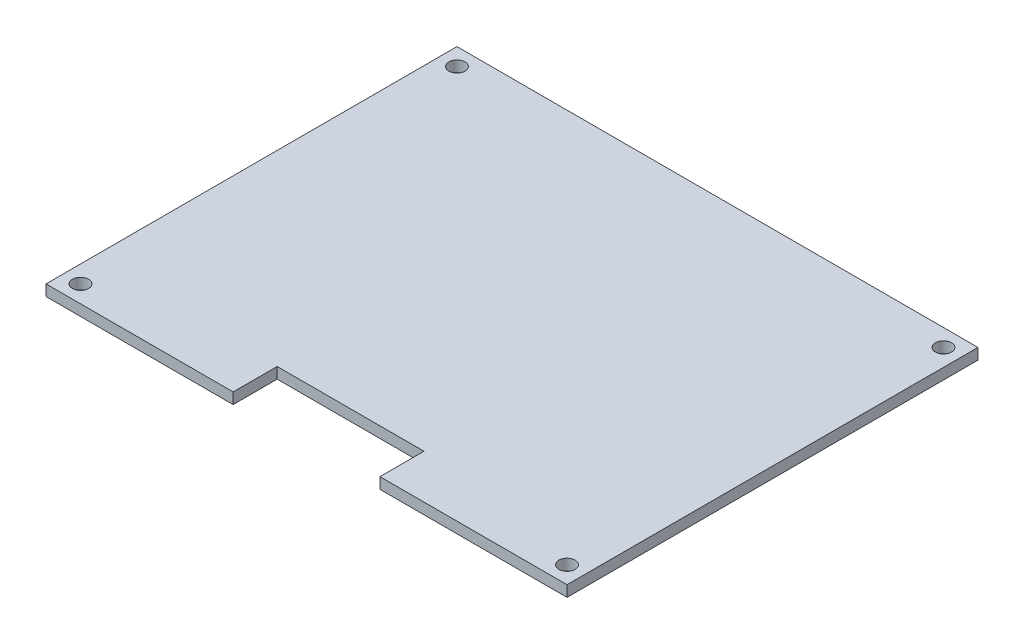
SolidWorks part; units mm, degrees
ref_plane "Front Plane" through (0, 0, 0) normal (0, 0, 1) x (1, 0, 0)
ref_plane "Top Plane" through (0, 0, 0) normal (0, 1, 0) x (1, 0, 0)
ref_plane "Right Plane" through (0, 0, 0) normal (1, 0, 0) x (0, 0, -1)
sketch "Sketch1" plane through (0, 0, 0) normal (0, 1, 0) x (1, 0, 0)
  line L1 (0, 0) -> (71, 0)
  line L2 (0, 0) -> (0, 56)
  line L3 (0, 56) -> (71, 56)
  line L4 (71, 0) -> (71, 56)
  dimension "D1" = 71
  dimension "D2" = 56
extrude "Boss-Extrude1" add sketch "Sketch1" along normal blind 1.5
sketch "Sketch2" plane through (0, 1.5, 0) normal (0, 1, 0) x (1, 0, 0)
  line L0 (0, 0) -> (71, 0) construction
  line L1 (25.5, 6) -> (45.5, 6)
  line L2 (25.5, 6) -> (25.5, 0)
  line L3 (25.5, 0) -> (45.5, 0)
  line L4 (45.5, 6) -> (45.5, 0)
  point P4 (35.5, 0)
  dimension "D1" = 20
  dimension "D2" = 6
extrude "Cut-Extrude1" cut sketch "Sketch2" against normal up to surface (1.5 mm away) up to face at (35.5, 0, -28)
sketch "Sketch5" plane through (0, 1.5, 0) normal (0, 1, 0) x (1, 0, 0)
  line L0 (2.35, 53.65) -> (2.35, 56) construction
  line L1 (71, 56) -> (0, 56) construction
  line L2 (2.35, 56) -> (2.35, 53.65) construction
  line L3 (2.35, 53.65) -> (0, 53.65) construction
  line L4 (0, 56) -> (0, 0) construction
  line L5 (68.65, 53.65) -> (68.65, 56) construction
  line L6 (71, 56) -> (0, 56) construction
  line L7 (68.65, 53.65) -> (71, 53.65) construction
  line L8 (71, 0) -> (71, 56) construction
  circle A0 centre (2.35, 53.65) radius 1.1
  circle A1 centre (68.65, 53.65) radius 1.1
  dimension "D1" = 2.2
  dimension "D3" = 2.35
extrude "Cut-Extrude2" cut sketch "Sketch5" against normal up to surface (1.5 mm away) up to face at (35.5, 0, -15.5)
ref_plane "Plane1" through (0, 0, -28) normal (0, 0, 1) x (1, 0, 0)
mirror "Mirror1" about plane through (0, 0, -28) normal (0, 0, 1) of "Cut-Extrude2"
sketch "Sketch6" plane through (0, 1.5, 0) normal (0, 1, 0) x (1, 0, 0)
  line L0 (63, 40) -> (71, 40) construction
  line L1 (71, 0) -> (71, 56) construction
  line L2 (63, 56) -> (63, 40) construction
  line L3 (71, 56) -> (0, 56) construction
  line L4 (63, 40) -> (63, 28) construction
  line L5 (63, 28) -> (63, 16) construction
  line L6 (0, 56) -> (0, 0) construction
  line L7 (18.45, 13) -> (24.45, 13)
  line L8 (18.45, 13) -> (18.45, 7)
  line L9 (18.45, 7) -> (24.45, 7)
  line L10 (24.45, 13) -> (24.45, 7)
  line L11 (32.5, 13) -> (38.5, 13)
  line L12 (32.5, 13) -> (32.5, 7)
  line L13 (32.5, 7) -> (38.5, 7)
  line L14 (38.5, 13) -> (38.5, 7)
  line L15 (46.55, 13) -> (52.55, 13)
  line L16 (46.55, 13) -> (46.55, 7)
  line L17 (46.55, 7) -> (52.55, 7)
  line L18 (52.55, 13) -> (52.55, 7)
  line L19 (18.45, 10) -> (0, 10) construction
  line L20 (24.45, 10) -> (32.5, 10) construction
  line L21 (38.5, 10) -> (46.55, 10) construction
  line L22 (0, 0) -> (25.5, 0) construction
  line L23 (8, 56) -> (8, 40) construction
  line L24 (5.1, 32) -> (10.9, 32)
  line L25 (5.1, 32) -> (5.1, 20.4)
  line L26 (5.1, 20.4) -> (10.9, 20.4)
  line L27 (10.9, 32) -> (10.9, 20.4)
  line L28 (71, 56) -> (0, 56) construction
  line L29 (8, 40) -> (8, 32) construction
  circle A0 centre (63, 40) radius 2.5
  circle A1 centre (63, 28) radius 2.5
  circle A2 centre (63, 16) radius 2.5
  circle A3 centre (8, 40) radius 2.5
  dimension "D1" = 5
  dimension "D2" = 8
  dimension "D3" = 16
  dimension "D4" = 12
  dimension "D5" = 18.45
  dimension "D6" = 6
  dimension "D7" = 8.05
  dimension "D8" = 10
  dimension "D9" = 8
  dimension "D10" = 11.6
  dimension "D11" = 5.8
  dimension "D12" = 8
  dimension "D13" = 16
extrude "Cut-Extrude3" [suppressed] cut sketch "Sketch6" against normal up to surface (1.5 mm away)
